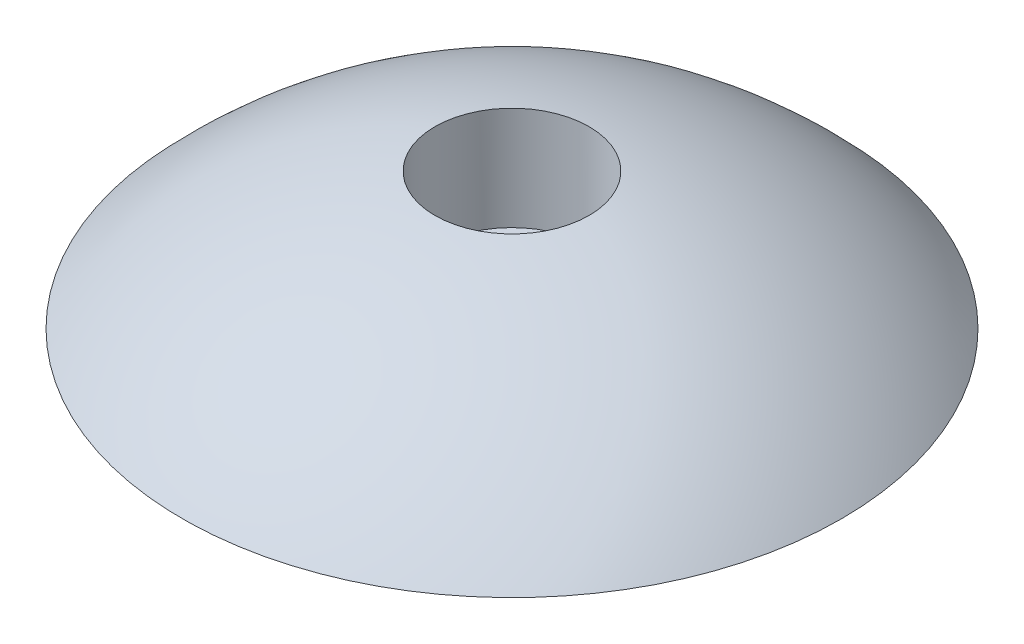
SolidWorks part; units mm, degrees
material "AISI 1015 Steel, Cold Drawn (SS)"
ref_plane "Front Plane" through (0, 0, 0) normal (0, 0, 1) x (1, 0, 0)
ref_plane "Top Plane" through (0, 0, 0) normal (0, 1, 0) x (1, 0, 0)
ref_plane "Right Plane" through (0, 0, 0) normal (1, 0, 0) x (0, 0, -1)
sketch "Sketch1" plane through (0, 0, 0) normal (0, 1, 0) x (1, 0, 0)
  line L0 (0, 20.5) -> (0, -20.5)
  arc A0 (0, 20.5) -> (0, -20.5) centre (0, 0) ccw
  dimension "D1" = 41
revolve "Revolve1" add sketch "Sketch1" angle 180 about L0
sketch "Sketch2" plane through (0, 0, 0) normal (0, -1, 0) x (1, 0, 0)
  circle A0 centre (0, 0) radius 20.5
  dimension "D1" = 41
extrude "Cut-Extrude1" cut sketch "Sketch2" against normal blind 14
ref_plane "Plane1" through (0, 20.5, 0) normal (0, 1, 0) x (1, 0, 0)
sketch "Sketch3" plane through (0, 20.5, 0) normal (0, 1, 0) x (1, 0, 0)
  circle A0 centre (0, 0) radius 3.5
  dimension "D1" = 7
extrude "Cut-Extrude2" cut sketch "Sketch3" against normal blind 5
sketch "Sketch4" plane through (0, 15.5, 0) normal (0, 1, 0) x (1, 0, 0)
  circle A0 centre (0, 0) radius 1.125
  dimension "D1" = 2.25
extrude "Cut-Extrude3" cut sketch "Sketch4" against normal through all
